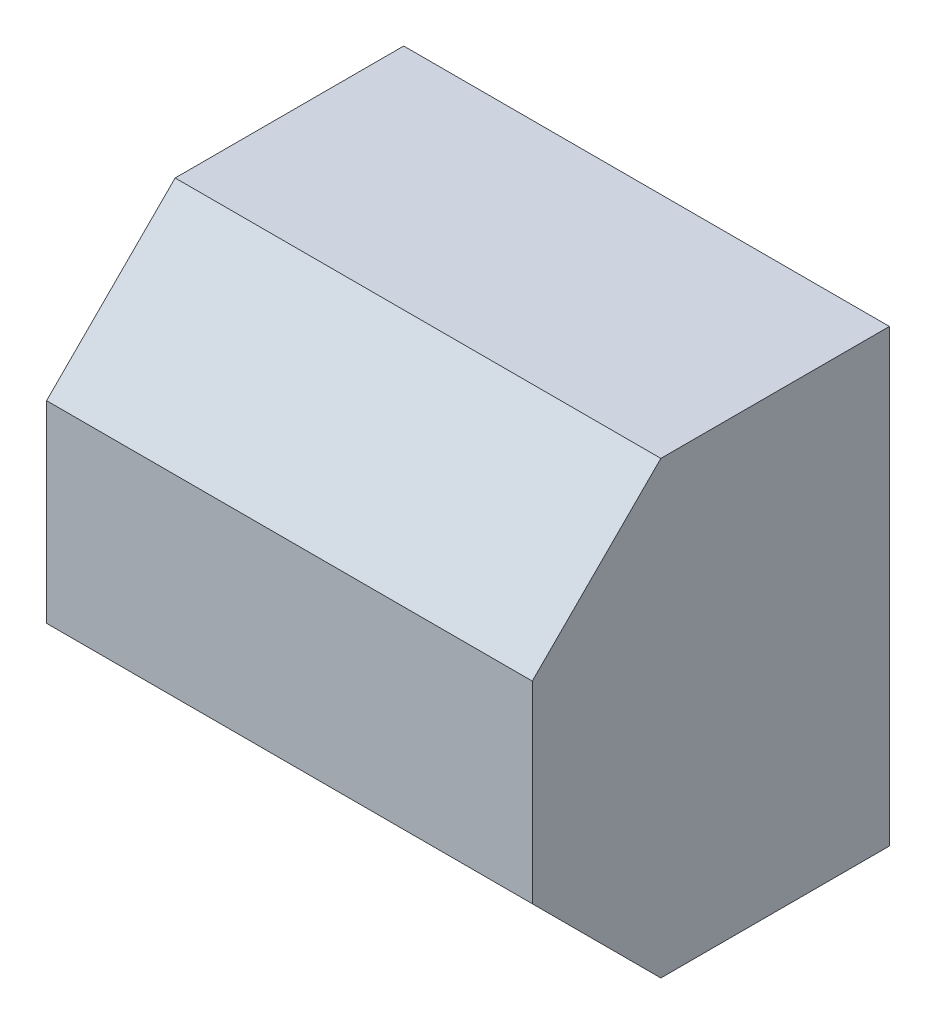
SolidWorks part; units mm, degrees
ref_plane "前视基准面" through (0, 0, 0) normal (0, 0, 1) x (1, 0, 0)
ref_plane "上视基准面" through (0, 0, 0) normal (0, 1, 0) x (1, 0, 0)
ref_plane "右视基准面" through (0, 0, 0) normal (1, 0, 0) x (0, 0, -1)
sketch "草图1" plane through (0, 0, 0) normal (0, 0, 1) x (1, 0, 0)
  line L1 (-5.5317, 2.5941) -> (1.2683, 2.5941)
  line L2 (-5.5317, 2.5941) -> (-5.5317, -3.7059)
  line L3 (-5.5317, -3.7059) -> (1.2683, -3.7059)
  line L4 (1.2683, 2.5941) -> (1.2683, -3.7059)
  dimension "D1" = 6.8
  dimension "D2" = 6.3
extrude "凸台-拉伸1" add sketch "草图1" along normal blind 5
chamfer "倒角1" distance 1.8 angle 45 2 edges at (-2.1317, -3.7059, 5) (-2.1317, 2.5941, 5)
